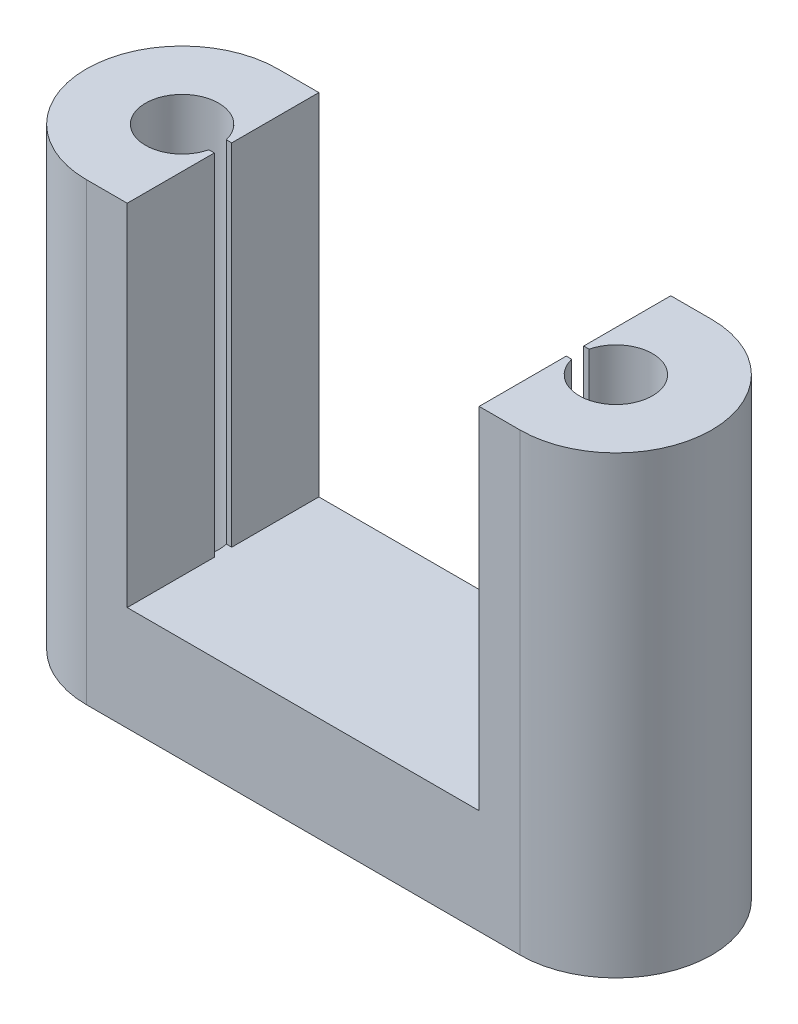
SolidWorks part; units mm, degrees
ref_plane "Front Plane" through (0, 0, 0) normal (0, 0, 1) x (1, 0, 0)
ref_plane "Top Plane" through (0, 0, 0) normal (0, 1, 0) x (1, 0, 0)
ref_plane "Right Plane" through (0, 0, 0) normal (1, 0, 0) x (0, 0, -1)
sketch "Sketch1" plane through (0, 0, 0) normal (0, 1, 0) x (1, 0, 0)
  line L0 (0, 5.5) -> (24.9, 5.5)
  line L1 (0, -5.5) -> (24.9, -5.5)
  arc A0 (0, 5.5) -> (0, -5.5) centre (0, 0) ccw
  circle A1 centre (0, 0) radius 2.1
  arc A2 (24.9, -5.5) -> (24.9, 5.5) centre (24.9, 0) ccw
  circle A3 centre (24.9, 0) radius 2.1
  dimension "D1" = 11
  dimension "D2" = 4.2
  dimension "D3" = 4.2
  dimension "D5" = 24.9
extrude "Boss-Extrude1" add sketch "Sketch1" along normal blind 6
sketch "Sketch2" plane through (0, 6, 0) normal (0, 1, 0) x (1, 0, 0)
  line L0 (22.55, 5.5) -> (22.55, 0.5)
  line L1 (24.9, 5.5) -> (0, 5.5) construction
  line L2 (0, -5.5) -> (24.9, -5.5) construction
  line L3 (2.35, 5.5) -> (2.35, 0.5)
  line L4 (22.8604, 0.5) -> (22.55, 0.5)
  line L5 (22.8604, -0.5) -> (22.55, -0.5)
  line L6 (2.35, -0.5) -> (2.0396, -0.5)
  line L7 (2.35, 0.5) -> (2.0396, 0.5)
  line L8 (22.55, -0.5) -> (22.55, -5.5)
  line L9 (22.55, 5.5) -> (24.9, 5.5)
  line L10 (22.55, -5.5) -> (24.9, -5.5)
  line L11 (2.35, -5.5) -> (0, -5.5)
  line L12 (2.35, 5.5) -> (0, 5.5)
  line L13 (2.35, -0.5) -> (2.35, -5.5)
  arc A0 (2.0396, 0.5) -> (2.0396, -0.5) centre (0, 0) ccw
  arc A1 (0, 5.5) -> (0, -5.5) centre (0, 0) ccw
  arc A2 (22.8604, -0.5) -> (22.8604, 0.5) centre (24.9, 0) ccw
  arc A3 (24.9, -5.5) -> (24.9, 5.5) centre (24.9, 0) ccw
  point P24 (22.7052, 0.5)
  dimension "D5" = 4.2
  dimension "D7" = 4.2
  dimension "D1" = 2.35
  dimension "D2" = 2.35
  dimension "D3" = 5
  dimension "D4" = 5
  dimension "D9" = 5
  dimension "D10" = 5
extrude "Boss-Extrude2" add sketch "Sketch2" along normal blind 20.1
